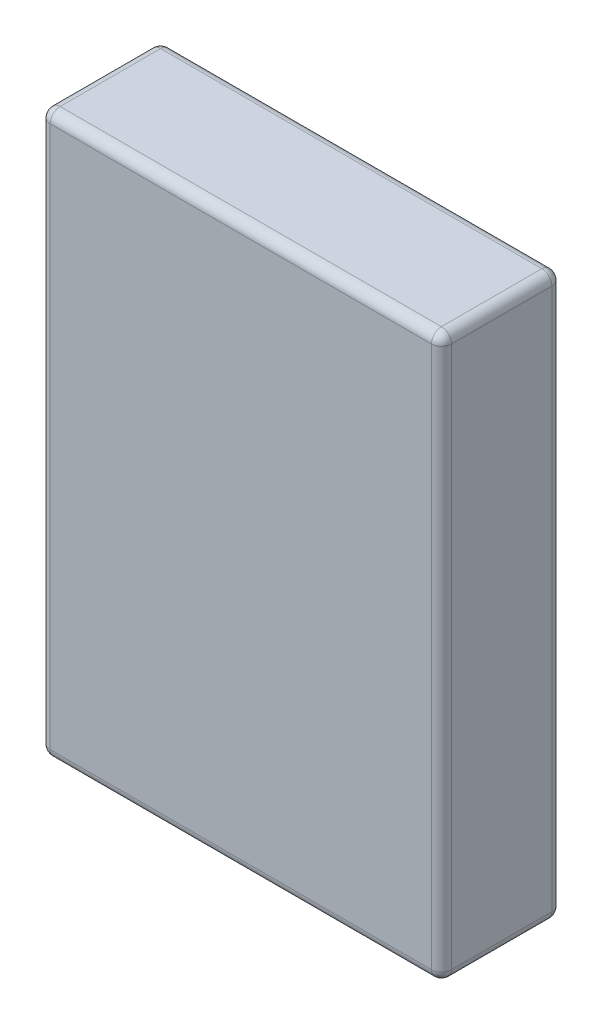
SolidWorks part; units mm, degrees
material "Polyurethane Foam Rigid"
ref_plane "Front" through (0, 0, 0) normal (0, 0, 1) x (1, 0, 0)
ref_plane "Top" through (0, 0, 0) normal (0, 1, 0) x (1, 0, 0)
ref_plane "Right" through (0, 0, 0) normal (1, 0, 0) x (0, 0, -1)
sketch "Sketch1" plane through (0, 0, 0) normal (0, 0, 1) x (1, 0, 0)
  line L1 (-63.5, 88.9) -> (63.5, 88.9)
  line L2 (-63.5, 88.9) -> (-63.5, -88.9)
  line L3 (-63.5, -88.9) -> (63.5, -88.9)
  line L4 (63.5, 88.9) -> (63.5, -88.9)
  line L5 (-63.5, 88.9) -> (63.5, -88.9) construction
  line L6 (-63.5, -88.9) -> (63.5, 88.9) construction
  point P0 (0, 0)
  dimension "D1" = 127
  dimension "D2" = 177.8
extrude "Boss-Extrude1" add sketch "Sketch1" along normal blind 38.1
fillet "Fillet1" radius 3.175 12 edges at (63.5, 88.9, 19.05) (-63.5, 88.9, 19.05) (-63.5, -88.9, 19.05) (63.5, -88.9, 19.05) (0, -88.9, 38.1) (-63.5, 0, 38.1) (0, 88.9, 38.1) (63.5, 0, 38.1) (0, -88.9, 0) (-63.5, 0, 0) (0, 88.9, 0) (63.5, 0, 0)
